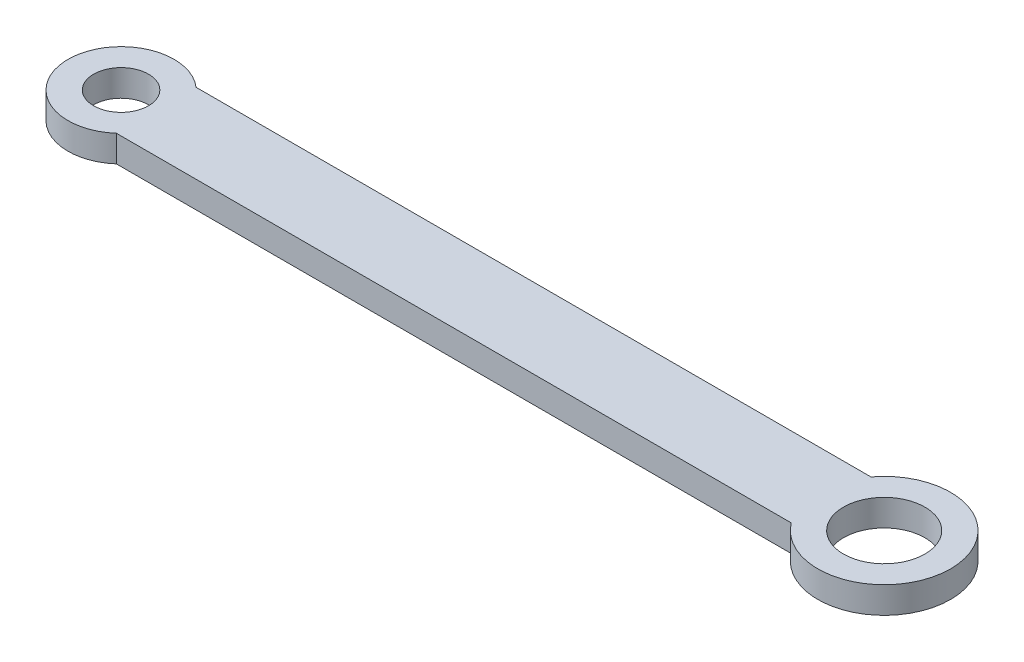
SolidWorks part; units mm, degrees
ref_plane "Front Plane" through (0, 0, 0) normal (0, 0, 1) x (1, 0, 0)
ref_plane "Top Plane" through (0, 0, 0) normal (0, 1, 0) x (1, 0, 0)
ref_plane "Right Plane" through (0, 0, 0) normal (1, 0, 0) x (0, 0, -1)
sketch "Sketch1" plane through (0, 0, 0) normal (0, 1, 0) x (1, 0, 0)
  line L0 (0, 4.5) -> (80.23, 4.5)
  line L1 (80.23, 4.5) -> (80.23, -4.5)
  line L2 (80.23, -4.5) -> (0, -4.5)
  line L3 (0, -4.5) -> (0, 4.5)
  circle A0 centre (0, 0) radius 3.1
  circle A1 centre (0, 0) radius 6
  circle A2 centre (86.23, 0) radius 4.6
  circle A3 centre (86.23, 0) radius 7.5
  dimension "D1" = 6.2
  dimension "D2" = 12
  dimension "D3" = 9.2
  dimension "D5" = 15
  dimension "D4" = 86.23
  dimension "D6" = 9
extrude "Boss-Extrude1" add sketch "Sketch1" along normal blind 3 contours L3 A1 A0 | L3 A1 A0 | A3 L0 A1 L2 | L1 A3 A2 | L1 A3 A2
